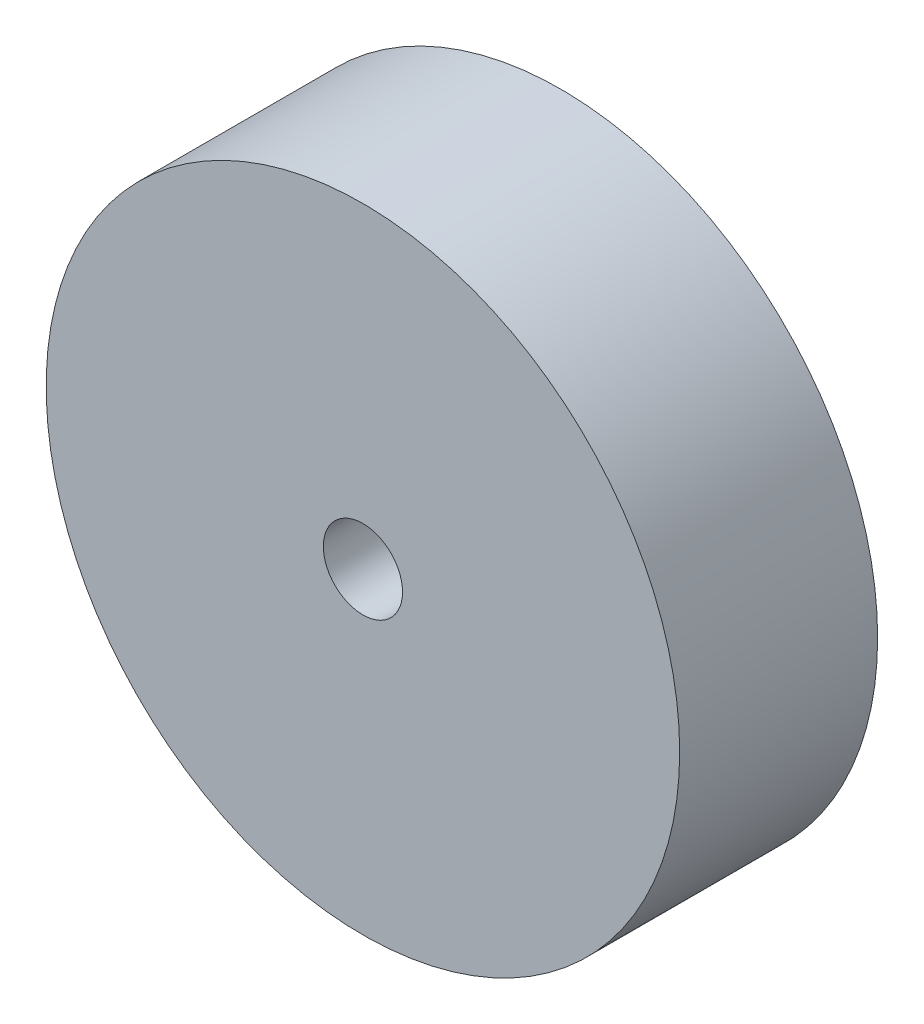
SolidWorks part; units mm, degrees
ref_plane "Alzado" through (0, 0, 0) normal (0, 0, 1) x (1, 0, 0)
ref_plane "Planta" through (0, 0, 0) normal (0, 1, 0) x (1, 0, 0)
ref_plane "Vista lateral" through (0, 0, 0) normal (1, 0, 0) x (0, 0, -1)
sketch "Croquis1" plane through (0, 0, 0) normal (0, 0, 1) x (1, 0, 0)
  circle A0 centre (0, 0) radius 20
  dimension "D1" = 40
extrude "Saliente-Extruir1" add sketch "Croquis1" along normal blind 12.5
sketch "Croquis2" plane through (0, 0, 12.5) normal (0, 0, 1) x (1, 0, 0)
  circle A0 centre (0, 0) radius 2.5
  dimension "D1" = 5
extrude "Cortar-Extruir1" cut sketch "Croquis2" against normal blind 12.5
